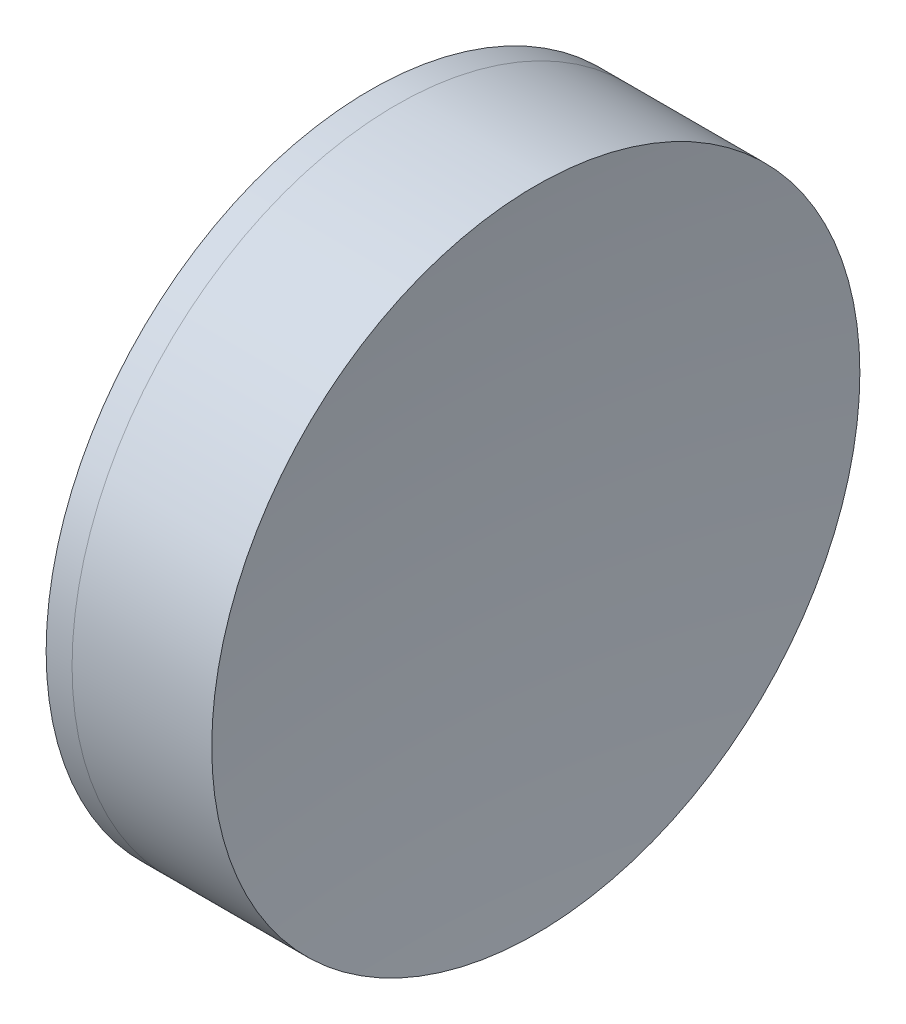
SolidWorks part; units mm, degrees
ref_plane "前视基准面" through (0, 0, 0) normal (0, 0, 1) x (1, 0, 0)
ref_plane "上视基准面" through (0, 0, 0) normal (0, 1, 0) x (1, 0, 0)
ref_plane "右视基准面" through (0, 0, 0) normal (1, 0, 0) x (0, 0, -1)
sketch "草图1" plane through (0, 0, 0) normal (0, 1, 0) x (1, 0, 0)
  line L0 (-0.8161, 0) -> (56.557, 0) construction
  line L1 (50.5816, -12.7) -> (51.5979, -12.7)
  line L2 (50.5816, 12.7) -> (51.5979, 12.7)
  arc A0 (51.5979, -12.7) -> (51.5979, 12.7) centre (5.8272, 0) ccw
  arc A1 (50.5816, 12.7) -> (50.5816, -12.7) centre (85.2272, 0) ccw
  point P10 (48.3272, 0)
  point P11 (53.3272, 0)
  dimension "D3" = 36.9
  dimension "D4" = 47.5
  dimension "D1" = 12.7
  dimension "D2" = 12.7
  dimension "D5" = 5
revolve "旋转1" add sketch "草图1" angle 360 about L0
sketch "草图2" plane through (0, 0, 0) normal (0, 1, 0) x (1, 0, 0)
  line L0 (-0.5519, 0) -> (62.1198, 0) construction
  line L2 (51.5979, 12.7) -> (57.0723, 12.7)
  line L3 (51.5979, -12.7) -> (57.0723, -12.7)
  arc A0 (57.0723, 12.7) -> (57.0723, -12.7) centre (164.9272, 0) ccw
  arc A1 (51.5979, -12.7) -> (51.5979, 12.7) centre (5.8272, 0) ccw construction
  arc A2 (51.5979, -12.7) -> (51.5979, 12.7) centre (5.8272, 0) ccw
  point P4 (53.3272, 0)
  point P8 (56.3272, 0)
  point P9 (62.1198, 0)
  dimension "D1" = 108.6
  dimension "D2" = 3
revolve "旋转2" add sketch "草图2" angle 360 about L0
